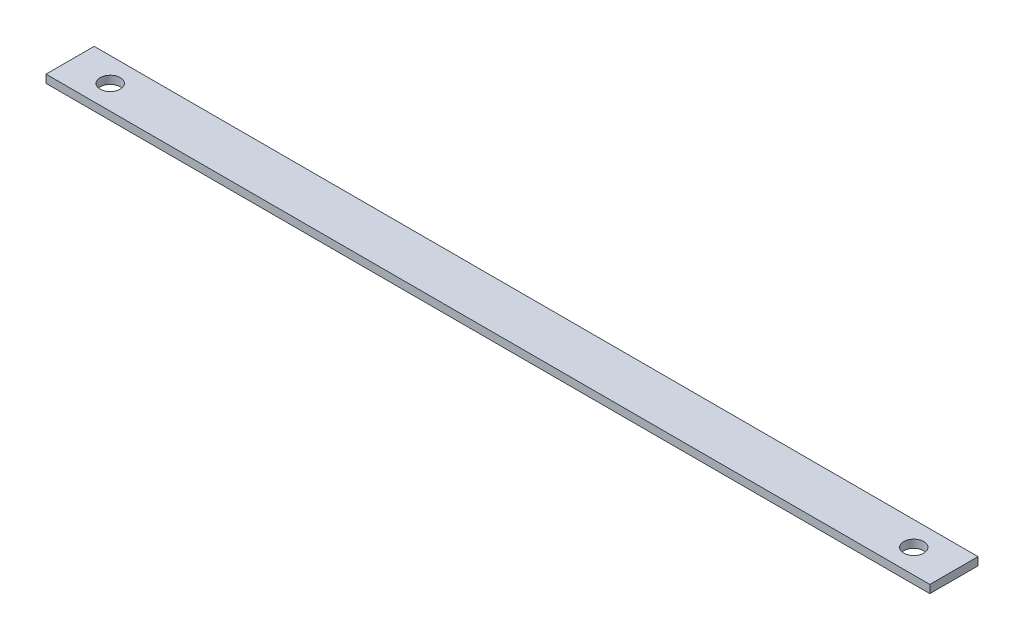
SolidWorks part; units mm, degrees
ref_plane "Front Plane" through (0, 0, 0) normal (0, 0, 1) x (1, 0, 0)
ref_plane "Top Plane" through (0, 0, 0) normal (0, 1, 0) x (1, 0, 0)
ref_plane "Right Plane" through (0, 0, 0) normal (1, 0, 0) x (0, 0, -1)
sketch "Sketch1" plane through (0, 0, 0) normal (0, 1, 0) x (1, 0, 0)
  line L1 (-110.0936, -6) -> (110.0936, -6)
  line L2 (-110.0936, -6) -> (-110.0936, 6)
  line L3 (-110.0936, 6) -> (110.0936, 6)
  line L4 (110.0936, -6) -> (110.0936, 6)
  line L5 (-110.0936, -6) -> (110.0936, 6) construction
  line L6 (-110.0936, 6) -> (110.0936, -6) construction
  point P0 (0, 0)
  dimension "D1" = 12
  dimension "D2" = 220.1872
extrude "Boss-Extrude1" add sketch "Sketch1" along normal blind 2
sketch "Sketch2" plane through (0, 2, 0) normal (0, 1, 0) x (1, 0, 0)
  line L0 (-93.3786, 0) -> (99.7379, 0) construction
  line L1 (0, 28.8342) -> (0, -18.9283) construction
  point P5 (100.0936, 0)
  point P6 (-100.0936, 0)
  dimension "D1" = 100.0936
hole_wizard "Ø5.0mm Dowel Hole1" positions "Sketch3" profile "Sketch4" hole size "Ø5.0" standard "ANSI Metric" end condition up to next
sketch "Sketch3" plane through (0, 2, 0) normal (0, 1, 0) x (1, 0, 0)
  point P0 (-100.0936, 0)
  point P3 (100.0936, 0)
sketch "Sketch4" plane through (-100.0936, 2, 0) normal (1, 0, 0) x (0, 0, 1)
  line L0 (0, 0) -> (0, 2)
  line L1 (0, 2) -> (2.5, 2)
  line L2 (2.5, 2) -> (2.5, 0)
  line L5 (2.5, 0) -> (0, 0)
  line L11 (0, -6.35) -> (0, 107.95) construction
  dimension "Thru Hole Dia." = 5
  dimension "Thru Hole Depth" = 2
equation "\"Width\"=12"
equation "\"Length\"= 200.18723"
equation "\"D2@Sketch1\"=\"Length\"+20"
equation "\"thick\"= 2"
equation "\"D1@Boss-Extrude1\"=\"thick\""
equation "\"D1@Sketch2\"=\"Length\"/2"
equation "\"D1@Sketch1\"=\"Width\""
